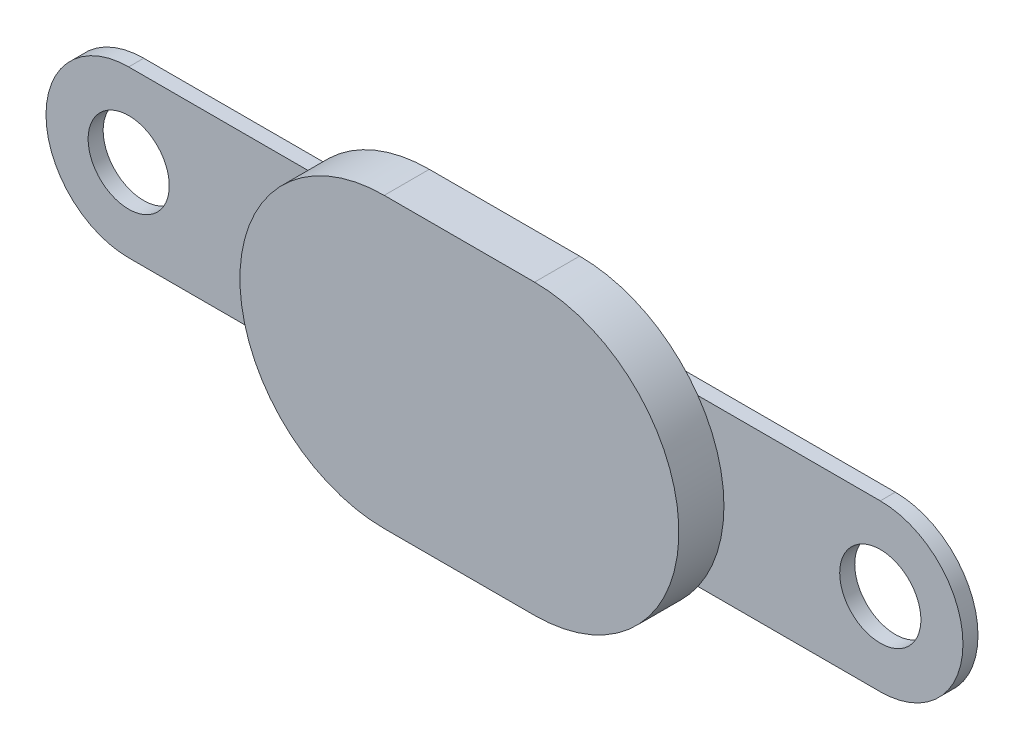
SolidWorks part; units mm, degrees
ref_plane "Front Plane" through (0, 0, 0) normal (0, 0, 1) x (1, 0, 0)
ref_plane "Top Plane" through (0, 0, 0) normal (0, 1, 0) x (1, 0, 0)
ref_plane "Right Plane" through (0, 0, 0) normal (1, 0, 0) x (0, 0, -1)
sketch "Sketch2" plane through (0, 0, 0) normal (0, 0, 1) x (1, 0, 0)
  line L0 (-2.5, -4.8) -> (2.5, -4.8)
  line L1 (2.5, 4.8) -> (-2.5, 4.8)
  arc A0 (-2.5, 4.8) -> (-2.5, -4.8) centre (-2.5, 0) ccw
  arc A1 (2.5, -4.8) -> (2.5, 4.8) centre (2.5, 0) ccw
  dimension "D1" = 4.8
  dimension "D2" = 2.5
  dimension "D3" = 2.5
extrude "Boss-Extrude2" add sketch "Sketch2" along normal blind 1.5
sketch "Sketch4" plane through (0, 0, 0) normal (0, 0, -1) x (-1, 0, 0)
  line L1 (-12.5, -2.75) -> (12.5, -2.75)
  line L2 (-12.5, -2.75) -> (-12.5, 2.75) construction
  line L3 (-12.5, 2.75) -> (12.5, 2.75)
  line L4 (12.5, -2.75) -> (12.5, 2.75) construction
  line L5 (-12.5, -2.75) -> (12.5, 2.75) construction
  line L6 (-12.5, 2.75) -> (12.5, -2.75) construction
  arc A4 (-12.5, 2.75) -> (-12.5, -2.75) centre (-12.5, 0) ccw
  arc A5 (12.5, 2.75) -> (12.5, -2.75) centre (12.5, 0) cw
  circle A6 centre (-12.5, 0) radius 1.35
  circle A7 centre (12.5, 0) radius 1.35
  point P0 (0, 0)
  dimension "D3" = 2.7
  dimension "D4" = 2.7
  dimension "D1" = 25
  dimension "D2" = 5.5
extrude "Boss-Extrude4" add sketch "Sketch4" along normal blind 0.5
